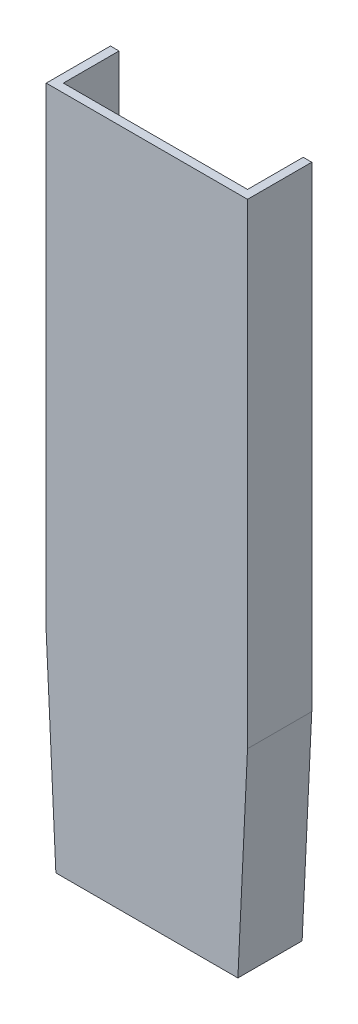
SolidWorks part; units mm, degrees
ref_plane "Płaszczyzna przednia" through (0, 0, 0) normal (0, 0, 1) x (1, 0, 0)
ref_plane "Płaszczyzna górna" through (0, 0, 0) normal (0, 1, 0) x (1, 0, 0)
ref_plane "Płaszczyzna prawa" through (0, 0, 0) normal (1, 0, 0) x (0, 0, -1)
sketch "Szkic1" plane through (0, 0, 0) normal (0, 0, 1) x (1, 0, 0)
  line L0 (-43.8993, 241.1087) -> (50.1007, 241.1087)
  line L1 (50.1007, 241.1087) -> (50.1007, 18.9325)
  line L2 (45.6007, -76.0675) -> (50.1007, 18.9325)
  line L4 (-43.8993, 18.9325) -> (-39.3993, -76.0675)
  line L5 (-43.8993, 18.9325) -> (-43.8993, 241.1087)
  line L8 (-39.3993, -76.0675) -> (45.6007, -76.0675)
  dimension "D1" = 94
  dimension "D2" = 95
extrude "Dodanie-wyciągnięcie1" add sketch "Szkic1" along normal blind 30
shell "Skorupa2" thickness 4
